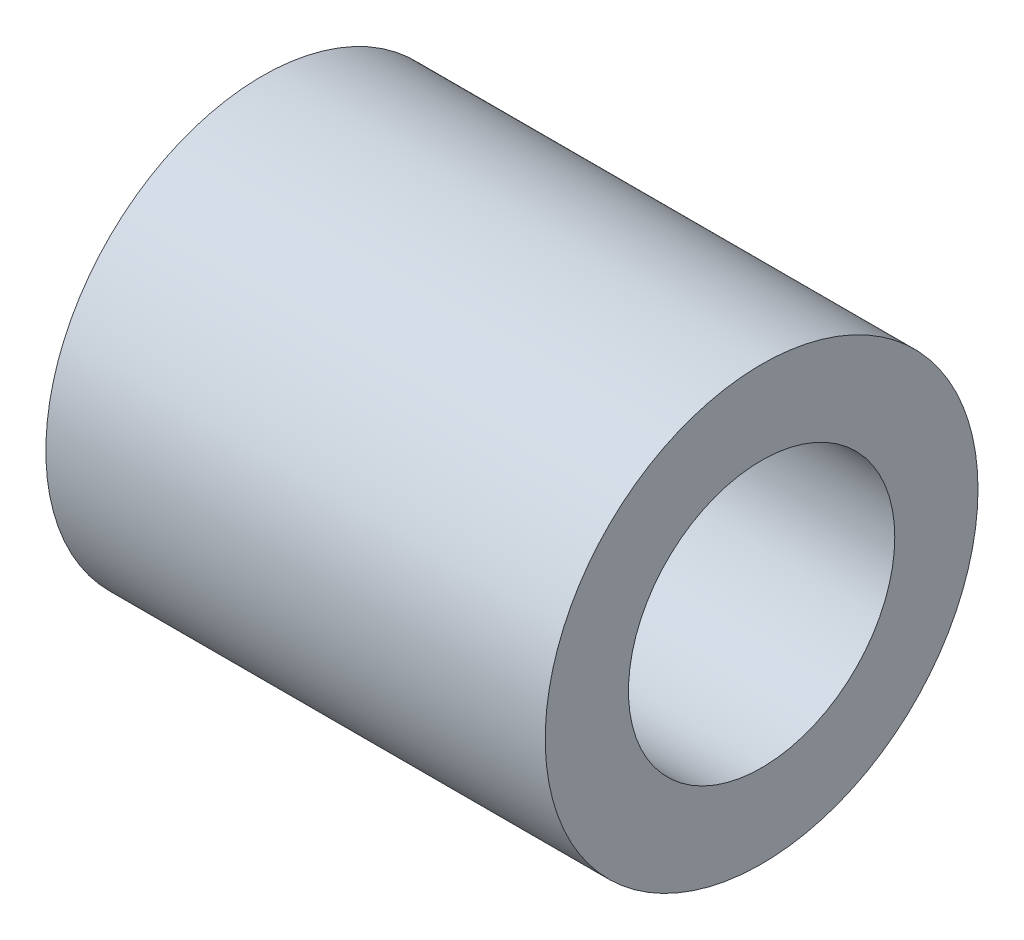
SolidWorks part; units mm, degrees
material "黄铜"
ref_plane "前视基准面" through (0, 0, 0) normal (0, 0, 1) x (1, 0, 0)
ref_plane "上视基准面" through (0, 0, 0) normal (0, 1, 0) x (1, 0, 0)
ref_plane "右视基准面" through (0, 0, 0) normal (1, 0, 0) x (0, 0, -1)
sketch "草图1" plane through (0, 0, 0) normal (1, 0, 0) x (0, 0, -1)
  circle A0 centre (0, 0) radius 8
  circle A1 centre (0, 0) radius 13
  dimension "D1" = 16
  dimension "D2" = 26
extrude "凸台-拉伸1" add sketch "草图1" against normal blind 30
